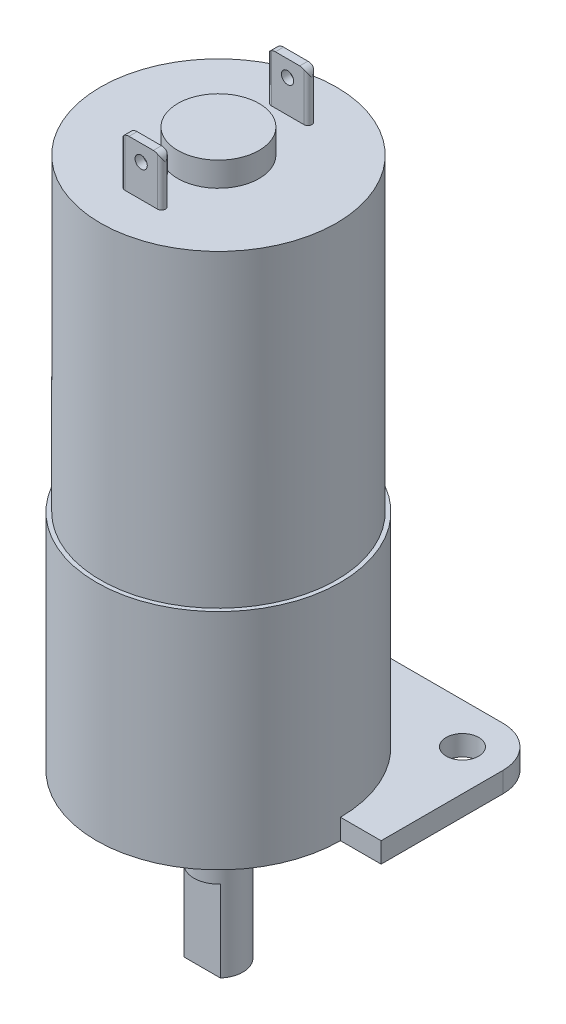
SolidWorks part; units mm, degrees
ref_plane "Alzado" through (0, 0, 0) normal (0, 0, 1) x (1, 0, 0)
ref_plane "Planta" through (0, 0, 0) normal (0, 1, 0) x (1, 0, 0)
ref_plane "Vista lateral" through (0, 0, 0) normal (1, 0, 0) x (0, 0, -1)
sketch "Croquis1" plane through (0, 0, 0) normal (0, 1, 0) x (1, 0, 0)
  circle A0 centre (0, 0) radius 14.5
  dimension "D1" = 29
extrude "Motor" add sketch "Croquis1" along normal blind 38
sketch "Croquis2" plane through (0, 38, 0) normal (0, 1, 0) x (1, 0, 0)
  circle A0 centre (0, 0) radius 5
  dimension "D1" = 10
extrude "Saliente posterior" add sketch "Croquis2" along normal blind 3
sketch "Croquis3" plane through (0, 38, 0) normal (0, 1, 0) x (1, 0, 0)
  line L0 (-11.3688, 9) -> (11.3688, 9) construction
  line L1 (-2, 9) -> (2, 9) construction
  line L2 (-2, 9.5) -> (2, 9.5)
  line L3 (-2, 8.5) -> (2, 8.5)
  line L4 (-14.5, 0) -> (14.5, 0) construction
  line L5 (-2, -9) -> (2, -9) construction
  line L6 (-2, -9.5) -> (2, -9.5)
  line L7 (-2, -8.5) -> (2, -8.5)
  circle A0 centre (0, 0) radius 14.5 construction
  arc A1 (-2, 9.5) -> (-2, 8.5) centre (-2, 9) ccw
  arc A2 (2, 8.5) -> (2, 9.5) centre (2, 9) ccw
  arc A3 (-2, -9.5) -> (-2, -8.5) centre (-2, -9) cw
  arc A4 (2, -8.5) -> (2, -9.5) centre (2, -9) cw
  point P7 (0, 9)
  point P17 (0, -9)
  dimension "D3" = 0.5
  dimension "D1" = 9
  dimension "D2" = 4
extrude "Bornes" add sketch "Croquis3" along normal blind 6
sketch "Croquis4" plane through (0, 0, 9.5) normal (0, 0, 1) x (1, 0, 0)
  line L0 (0, 44) -> (0, 38) construction
  line L1 (-2, 44) -> (2, 44) construction
  line L2 (-2, 38) -> (2, 38) construction
  line L3 (-2.5, 43) -> (2.5, 43) construction
  line L4 (-2.5, 44) -> (-2.5, 38) construction
  line L5 (2.5, 38) -> (2.5, 44) construction
  line L6 (-1.5, 44) -> (-1.5, 38) construction
  line L7 (14.5, 38) -> (-14.5, 38) construction
  line L8 (-2, 44) -> (-2.5, 44) construction
  line L9 (2.5, 43) -> (2.5, 44)
  line L10 (2.5, 44) -> (1.5, 44)
  line L11 (-2.5, 43) -> (-2.5, 44)
  line L12 (-2.5, 44) -> (-1.5, 44)
  arc A0 (-2.5, 43) -> (-1.5, 44) centre (-1.5, 43) cw
  arc A1 (2.5, 43) -> (1.5, 44) centre (1.5, 43) ccw
  circle A2 centre (0, 42) radius 0.75
  line M2 (2, 38) -> (2, 44)
  line M3 (2, 44) -> (-2, 44)
  line M4 (-2, 44) -> (-2, 38)
  dimension "D3" = 1.5
  dimension "D1" = 1
  dimension "D2" = 1
  dimension "D4" = 2
extrude "Agujero Bornes" cut sketch "Croquis4" against normal through all contours A2 | A1 L9 L10 M2 | A1 M2 M3 | L11 A0 L12 M4 | A0 M4 M3
sketch "Croquis5" plane through (0, 0, 0) normal (0, -1, 0) x (1, 0, 0)
  circle A0 centre (0, 0) radius 15
  dimension "D1" = 30
extrude "Caja reductora" add sketch "Croquis5" along normal blind 25
sketch "Croquis6" plane through (0, -25, 0) normal (0, -1, 0) x (1, 0, 0)
  line L1 (-15, 20) -> (15, 20)
  line L2 (-20, 15) -> (-20, -15)
  line L3 (-15, -20) -> (15, -20)
  line L4 (20, 15) -> (20, -15)
  line L5 (-20, 20) -> (20, -20) construction
  line L6 (-20, -20) -> (20, 20) construction
  circle A0 centre (-15, 15) radius 2
  circle A1 centre (15, 15) radius 2
  circle A2 centre (15, -15) radius 2
  circle A3 centre (-15, -15) radius 2
  arc A4 (-20, -15) -> (-15, -20) centre (-15, -15) ccw
  arc A5 (15, -20) -> (20, -15) centre (15, -15) ccw
  arc A6 (15, 20) -> (20, 15) centre (15, 15) cw
  arc A7 (-15, 20) -> (-20, 15) centre (-15, 15) ccw
  point P0 (0, 0)
  point P17 (0, 0)
  dimension "D3" = 4
  dimension "D6" = 5
  dimension "D1" = 40
  dimension "D2" = 40
  dimension "D4" = 5
  dimension "D5" = 4
extrude "Brida" add sketch "Croquis6" along normal blind 2.5
sketch "Croquis7" plane through (0, -27.5, 0) normal (0, -1, 0) x (1, 0, 0)
  circle A0 centre (0, 0) radius 6.5
  dimension "D1" = 13
extrude "Saliente eje" add sketch "Croquis7" along normal blind 3
sketch "Croquis8" plane through (0, -30.5, 0) normal (0, -1, 0) x (1, 0, 0)
  circle A0 centre (0, 0) radius 3
  dimension "D1" = 6
extrude "Eje" add sketch "Croquis8" along normal blind 17
sketch "Croquis9" plane through (0, -47.5, 0) normal (0, -1, 0) x (1, 0, 0)
  line L0 (-2.2361, 2) -> (2.2361, 2)
  circle A0 centre (0, 0) radius 3 construction
  circle A1 centre (0, 0) radius 3
  circle M1 centre (0, 0) radius 3
  dimension "D1" = 2
extrude "Corte Plano eje" cut sketch "Croquis9" against normal blind 10 contours L0 M1
sketch "Croquis10" plane through (0, -25, 0) normal (0, 1, 0) x (1, 0, 0)
  line L0 (-20, -15) -> (-20, 15) construction
  line L1 (-20, 0) -> (20, 0)
  line L2 (-20, 0) -> (-20, -20.4185)
  line L3 (-20, -20.4185) -> (20, -20.4185)
  line L4 (20, 0) -> (20, -20.4185)
  circle A0 centre (0, 0) radius 15
  circle M2 centre (15, -15) radius 2
  line M4 (-20, 15) -> (-20, -15)
  arc M5 (-20, -15) -> (-15, -20) centre (-15, -15) ccw
  line M6 (-15, -20) -> (15, -20)
  arc M7 (15, -20) -> (20, -15) centre (15, -15) ccw
  line M8 (20, -15) -> (20, 15)
  circle M11 centre (-15, -15) radius 2
  circle M13 centre (0, 0) radius 15
extrude "Corte Brida" cut sketch "Croquis10" against normal blind 10 contours L1 M4 M5 M6 M7 M8 M13 M2 M11
